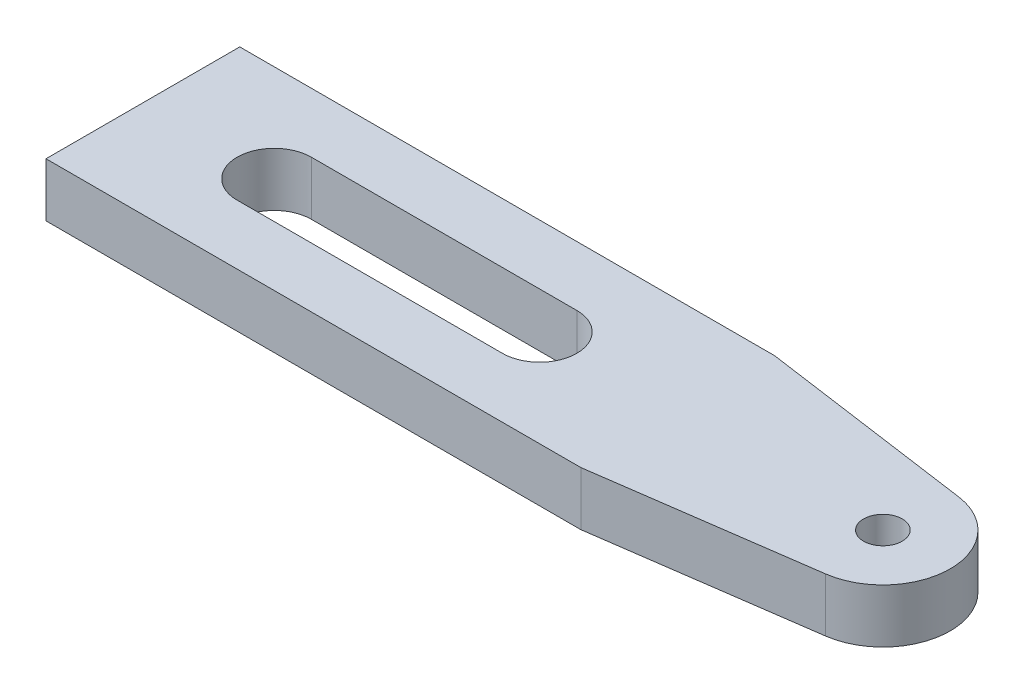
SolidWorks part; units mm, degrees
ref_plane "Front Plane" through (0, 0, 0) normal (0, 0, 1) x (1, 0, 0)
ref_plane "Top Plane" through (0, 0, 0) normal (0, 1, 0) x (1, 0, 0)
ref_plane "Right Plane" through (0, 0, 0) normal (1, 0, 0) x (0, 0, -1)
sketch "Sketch1" plane through (0, 0, 0) normal (0, 1, 0) x (1, 0, 0)
  line L0 (-15.24, 3.6576) -> (-15.24, -3.6576)
  line L1 (-15.24, -3.6576) -> (4.953, -3.6576)
  line L2 (4.953, -3.6576) -> (13.0547, -2.5151)
  line L3 (4.953, 3.6576) -> (13.0547, 2.5151)
  line L4 (-15.24, 3.6576) -> (4.953, 3.6576)
  line L5 (-15.24, 0) -> (15.24, 0) construction
  arc A0 (13.0547, -2.5151) -> (13.0547, 2.5151) centre (12.7, 0) ccw
  point P5 (0, 0)
  dimension "D1" = 30.48
  dimension "D3" = 2.54
  dimension "D2" = 7.3152
  dimension "D4" = 20.193
extrude "Boss-Extrude1" add sketch "Sketch1" along normal blind 2.032
sketch "Sketch2" plane through (0, 2.032, 0) normal (0, 1, 0) x (1, 0, 0)
  line L0 (-10.2806, 0) -> (-0.2603, 0) construction
  line L1 (-10.2806, 1.4034) -> (-0.2603, 1.4034)
  line L2 (-10.2806, -1.4034) -> (-0.2603, -1.4034)
  line L3 (-15.24, 3.6576) -> (-15.24, -3.6576) construction
  arc A0 (-10.2806, 1.4034) -> (-10.2806, -1.4034) centre (-10.2806, 0) ccw
  arc A1 (-0.2603, -1.4034) -> (-0.2603, 1.4034) centre (-0.2603, 0) ccw
  point P2 (-5.2705, 0)
  point P8 (-15.24, 0)
  dimension "D1" = 12.827
  dimension "D3" = 3.556
  dimension "D2" = 2.8067
extrude "Cut-Extrude1" cut sketch "Sketch2" against normal up to next
sketch "Sketch3" plane through (0, 2.032, 0) normal (0, 1, 0) x (1, 0, 0)
  circle A0 centre (12.7, 0) radius 0.7302
  dimension "D1" = 1.4605
extrude "Cut-Extrude2" cut sketch "Sketch3" against normal up to next
